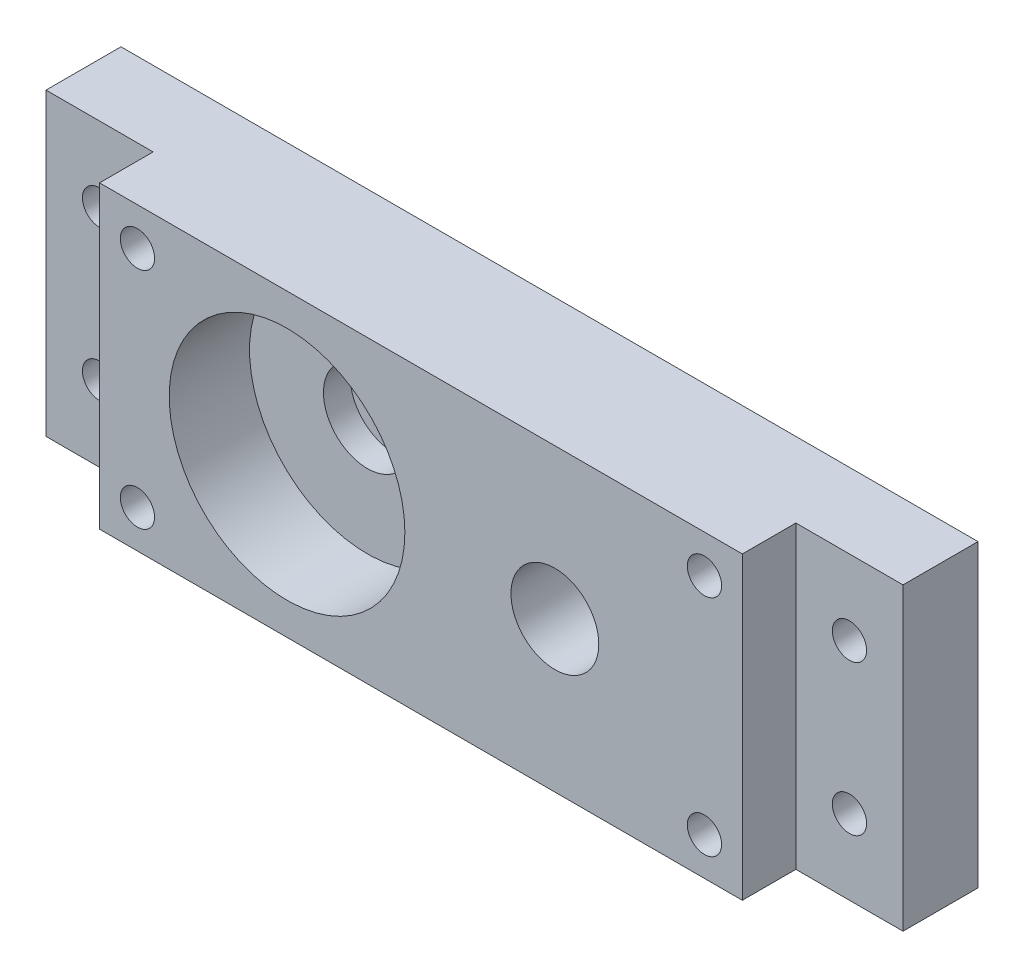
SolidWorks part; units mm, degrees
ref_plane "Front Plane" through (0, 0, 0) normal (0, 0, 1) x (1, 0, 0)
ref_plane "Top Plane" through (0, 0, 0) normal (0, 1, 0) x (1, 0, 0)
ref_plane "Right Plane" through (0, 0, 0) normal (1, 0, 0) x (0, 0, -1)
sketch "Sketch1" plane through (0, 0, 0) normal (0, 0, 1) x (1, 0, 0)
  line L0 (-30, 0) -> (30, 0) construction
  line L1 (30, -14) -> (-30, -14)
  line L2 (30, -14) -> (30, 14)
  line L3 (30, 14) -> (-30, 14)
  line L4 (-30, -14) -> (-30, 14)
  line L5 (30, -14) -> (-30, 14) construction
  line L6 (30, 14) -> (-30, -14) construction
  line L7 (-30, 14) -> (-25.155, 9.155) construction
  line L8 (-30, -14) -> (-23.8174, -7.8174) construction
  line L9 (0, 14) -> (0, 10.472) construction
  circle A0 centre (12.5, 0) radius 4.1
  circle A1 centre (-12.5, 0) radius 4.1
  circle A2 centre (-26.4645, 10.4645) radius 1.6
  circle A3 centre (-26.4645, -10.4645) radius 1.6
  circle A4 centre (26.4645, -10.4645) radius 1.6
  circle A5 centre (26.4645, 10.4645) radius 1.6
  point P0 (0, 0)
  dimension "D3" = 25
  dimension "D4" = 8.2
  dimension "D5" = 8.2
  dimension "D7" = 3.2
  dimension "D8" = 3.2
  dimension "D1" = 28
  dimension "D2" = 60
  dimension "D6" = 12.5
  dimension "D9" = 5
  dimension "D10" = 5
  dimension "D11" = 3.5355
  dimension "D12" = 3.5355
extrude "Boss-Extrude1" add sketch "Sketch1" along normal blind 10
sketch "Sketch2" plane through (0, 0, 10) normal (0, 0, 1) x (1, 0, 0)
  circle A0 centre (-12.5, 0) radius 11
  dimension "D1" = 22
extrude "Cut-Extrude1" cut sketch "Sketch2" against normal blind 7.5
sketch "Sketch3" plane through (0, 0, 0) normal (0, 0, -1) x (-1, 0, 0)
  line L0 (-35, 0) -> (-35, 14) construction
  line L1 (-30, 14) -> (-40, 14)
  line L3 (-30, -14) -> (-40, -14)
  line L4 (30, -14) -> (30, 14)
  line L5 (30, 14) -> (-30, 14)
  line L6 (-30, 14) -> (-30, -14)
  line L7 (-30, -14) -> (30, -14)
  line L9 (30, 14) -> (-30, 14)
  line L11 (-30, -14) -> (30, -14)
  line L12 (-40, 14) -> (-40, -14)
  line L13 (-30, 14) -> (-40, -14) construction
  line L14 (-30, -14) -> (-40, 14) construction
  line L15 (30, 14) -> (40, 14)
  line L17 (30, -14) -> (40, -14)
  line L18 (40, 14) -> (40, -14)
  line L19 (30, 14) -> (40, -14) construction
  line L20 (30, -14) -> (40, 14) construction
  line L21 (-35, 0) -> (-35, -14) construction
  line L22 (0, 14) -> (0, 8.5237) construction
  circle A0 centre (-35, 7) radius 1.6
  circle A1 centre (-35, -7) radius 1.6
  circle A2 centre (35, -7) radius 1.6
  circle A3 centre (35, 7) radius 1.6
  point P6 (-35, 0)
  point P9 (35, 0)
  dimension "D4" = 3.2
  dimension "D5" = 3.2
  dimension "D2" = 10
  dimension "D3" = 10
  dimension "D1" = 0
extrude "Boss-Extrude2" add sketch "Sketch3" along normal blind 2
sketch "Sketch4" plane through (0, 0, 0) normal (0, 0, 1) x (1, 0, 0)
  line L0 (30, 14) -> (30, -14) construction
  line L1 (30, -14) -> (40, -14) construction
  line L2 (40, -14) -> (40, 14) construction
  line L3 (40, 14) -> (30, 14) construction
  line L4 (-30, -14) -> (-30, 14) construction
  line L5 (-30, 14) -> (-40, 14) construction
  line L6 (-40, 14) -> (-40, -14) construction
  line L7 (-40, -14) -> (-30, -14) construction
  line L8 (30, 14) -> (30, -14)
  line L9 (30, -14) -> (40, -14)
  line L10 (40, -14) -> (40, 14)
  line L11 (40, 14) -> (30, 14)
  line L12 (-30, -14) -> (-30, 14)
  line L13 (-30, 14) -> (-40, 14)
  line L14 (-40, 14) -> (-40, -14)
  line L15 (-40, -14) -> (-30, -14)
  circle A0 centre (35, -7) radius 1.6 construction
  circle A1 centre (35, 7) radius 1.6 construction
  circle A2 centre (-35, -7) radius 1.6 construction
  circle A3 centre (-35, 7) radius 1.6 construction
  circle A4 centre (35, -7) radius 1.6
  circle A5 centre (35, 7) radius 1.6
  circle A6 centre (-35, -7) radius 1.6
  circle A7 centre (-35, 7) radius 1.6
extrude "Boss-Extrude3" add sketch "Sketch4" along normal offset from surface (5 mm away) 5 up to face at (-1.5, 0, 10)
